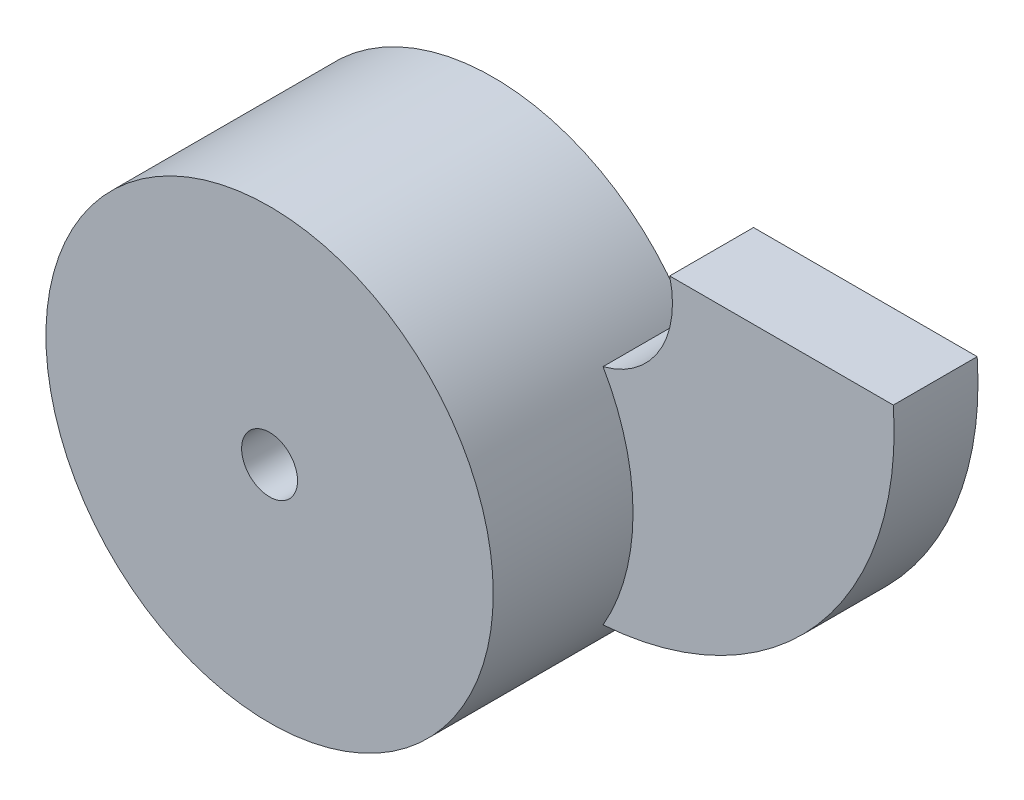
SolidWorks part; units mm, degrees
ref_plane "Front Plane" through (0, 0, 0) normal (0, 0, 1) x (1, 0, 0)
ref_plane "Top Plane" through (0, 0, 0) normal (0, 1, 0) x (1, 0, 0)
ref_plane "Right Plane" through (0, 0, 0) normal (1, 0, 0) x (0, 0, -1)
sketch "Sketch1" plane through (0, 0, 0) normal (0, 0, 1) x (1, 0, 0)
  line L0 (0, 0) -> (40, 0)
  line L1 (-46.5491, -20) -> (-46.5491, -60) construction
  line L2 (-46.5491, -40) -> (-20, -40) construction
  line L3 (0, 0) -> (-100.2458, 0) construction
  arc A0 (-11.9081, -20) -> (-11.9081, -60) centre (-46.5491, -40) ccw
  arc A1 (20, 0) -> (-20, -40) centre (-15.9541, -4.0459) cw construction
  arc A2 (0, 0) -> (-11.9081, -20) centre (-15.9541, -4.0459) cw
  arc A3 (40, 0) -> (-11.9081, -60) centre (-15.9541, -4.0459) cw
  circle A4 centre (-46.5491, -40) radius 5
  point P5 (20, 0)
  point P11 (-46.5491, -40)
  dimension "D1" = 80
  dimension "D4" = 10
  dimension "D2" = 40
  dimension "D3" = 40
extrude "Boss-Extrude1" add sketch "Sketch1" along normal blind 15
sketch "Sketch5" plane through (0, 0, 15) normal (0, 0, 1) x (1, 0, 0)
  circle A0 centre (-46.5491, -40) radius 40
  circle A1 centre (-46.5491, -40) radius 5
  dimension "D1" = 80
  dimension "D2" = 10
extrude "Boss-Extrude2" add sketch "Sketch5" along normal blind 25 contours A0 | A1
